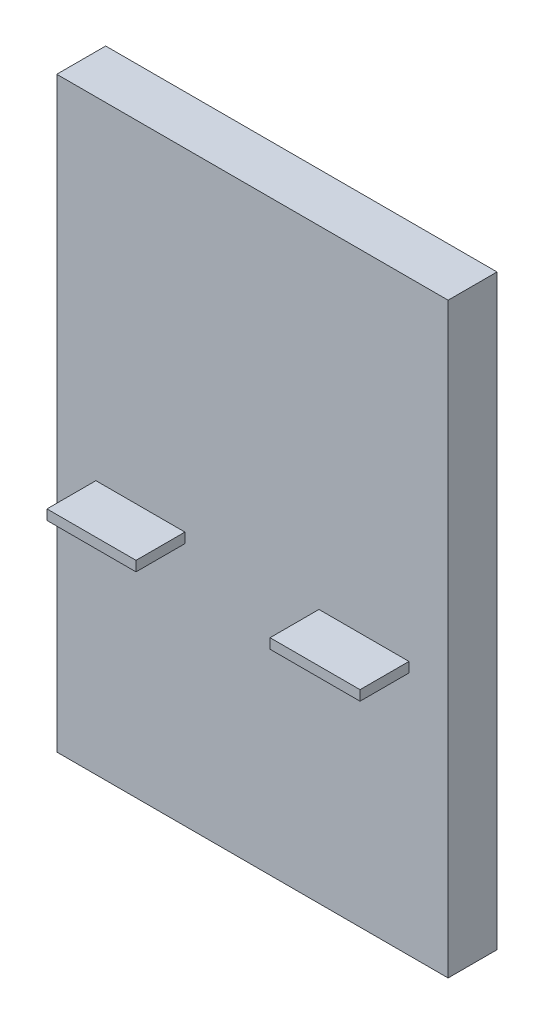
SolidWorks part; units mm, degrees
ref_plane "Front Plane" through (0, 0, 0) normal (0, 0, 1) x (1, 0, 0)
ref_plane "Top Plane" through (0, 0, 0) normal (0, 1, 0) x (1, 0, 0)
ref_plane "Right Plane" through (0, 0, 0) normal (1, 0, 0) x (0, 0, -1)
sketch "Sketch1" plane through (0, 0, 0) normal (0, 0, 1) x (1, 0, 0)
  line L1 (-1, 0) -> (1, 0)
  line L2 (-1, 0) -> (-1, 3)
  line L3 (-1, 3) -> (1, 3)
  line L4 (1, 0) -> (1, 3)
  dimension "D1" = 2
  dimension "D2" = 1
  dimension "D3" = 1
  dimension "D4" = 3
extrude "Boss-Extrude1" add sketch "Sketch1" against normal blind 0.25
sketch "Sketch2" plane through (0, 0, 0) normal (0, 0, 1) x (1, 0, 0)
  line L0 (-1, 0) -> (1, 0) construction
  line L1 (-0.8, 1.25) -> (-0.345, 1.25)
  line L2 (-0.8, 1.25) -> (-0.8, 1.3012)
  line L3 (-0.8, 1.3012) -> (-0.345, 1.3012)
  line L4 (-0.345, 1.25) -> (-0.345, 1.3012)
  line L5 (-1, 3) -> (-1, 0) construction
  line L6 (1, 0) -> (1, 3) construction
  line L7 (0.34, 1.3012) -> (0.8, 1.3012)
  line L8 (0.34, 1.3012) -> (0.34, 1.25)
  line L9 (0.34, 1.25) -> (0.8, 1.25)
  line L10 (0.8, 1.3012) -> (0.8, 1.25)
  point P4 (-0.5725, 1.25)
  dimension "D1" = 1.25
  dimension "D2" = 0.0512
  dimension "D3" = 0.2
  dimension "D4" = 0.2
  dimension "D5" = 0.0512
  dimension "D6" = 0.46
  dimension "D7" = 1.25
  dimension "D8" = 0.685
extrude "Boss-Extrude2" add sketch "Sketch2" along normal blind 0.25
